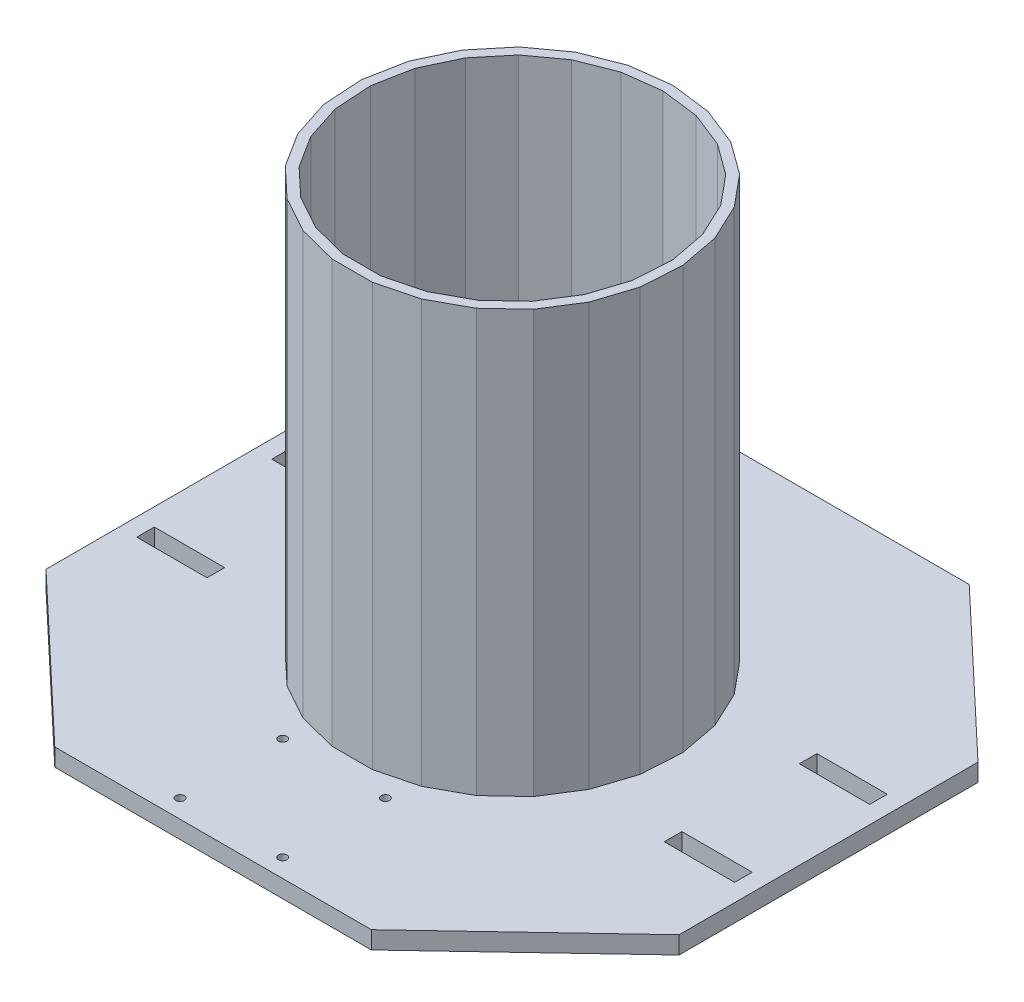
SolidWorks part; units mm, degrees
ref_plane "Front Plane" through (0, 0, 0) normal (0, 0, 1) x (1, 0, 0)
ref_plane "Top Plane" through (0, 0, 0) normal (0, 1, 0) x (1, 0, 0)
ref_plane "Right Plane" through (0, 0, 0) normal (1, 0, 0) x (0, 0, -1)
sketch "Sketch1" plane through (0, 0, 0) normal (0, 1, 0) x (1, 0, 0)
  line L1 (0, 0) -> (228.6, 0)
  line L2 (0, 0) -> (0, 215.9)
  line L3 (0, 215.9) -> (228.6, 215.9)
  line L4 (228.6, 0) -> (228.6, 215.9)
  dimension "D1" = 228.6
  dimension "D2" = 215.9
extrude "Boss-Extrude1" add sketch "Sketch1" along normal blind 6.35 contours L3 L4 L1 L2
sketch "Sketch14" plane through (0, 6.35, 0) normal (0, 1, 0) x (1, 0, 0)
  line L1 (0, 215.9) -> (228.6, 215.9) construction
  line L2 (0, 0) -> (228.6, 0) construction
  line L3 (0, 161.925) -> (228.6, 161.925) construction
  line L4 (0, 0) -> (0, 215.9) construction
  line L5 (228.6, 0) -> (228.6, 215.9) construction
  line L6 (0, 53.975) -> (228.6, 53.975) construction
  line L7 (57.15, 215.9) -> (57.15, 0) construction
  line L8 (171.45, 215.9) -> (171.45, 0) construction
sketch "Sketch13" plane through (0, 6.35, 0) normal (0, 1, 0) x (1, 0, 0)
  line L0 (0, 107.95) -> (228.6, 107.95) construction
  line L1 (0, 0) -> (0, 215.9) construction
  line L2 (228.6, 0) -> (228.6, 215.9) construction
  line L3 (0, 215.9) -> (0, 161.925)
  line L4 (0, 161.925) -> (57.15, 215.9)
  line L5 (57.15, 215.9) -> (0, 215.9)
  line L6 (114.3, 215.9) -> (114.3, 0) construction
  line L7 (0, 215.9) -> (228.6, 215.9) construction
  line L8 (0, 0) -> (228.6, 0) construction
  line L9 (228.6, 161.925) -> (171.45, 215.9)
  line L10 (228.6, 215.9) -> (228.6, 161.925)
  line L11 (171.45, 215.9) -> (228.6, 215.9)
  line L12 (228.6, 0) -> (228.6, 53.975)
  line L13 (171.45, 0) -> (228.6, 0)
  line L14 (228.6, 53.975) -> (171.45, 0)
  line L15 (0, 53.975) -> (57.15, 0)
  line L16 (0, 0) -> (0, 53.975)
  line L17 (57.15, 0) -> (0, 0)
sketch "Sketch8" plane through (0, 6.35, 0) normal (0, 1, 0) x (1, 0, 0)
  line L0 (0, 107.95) -> (228.6, 107.95) construction
  line L1 (6.35, 135.509) -> (31.75, 135.509)
  line L2 (6.35, 135.509) -> (6.35, 129.159)
  line L3 (6.35, 129.159) -> (31.75, 129.159)
  line L4 (31.75, 135.509) -> (31.75, 129.159)
  line L5 (0, 0) -> (0, 215.9) construction
  line L6 (228.6, 0) -> (228.6, 215.9) construction
  line L11 (114.3, 215.9) -> (114.3, 0) construction
  line L12 (0, 215.9) -> (228.6, 215.9) construction
  line L13 (0, 0) -> (228.6, 0) construction
  line L18 (222.25, 129.159) -> (196.85, 129.159)
  line L19 (196.85, 135.509) -> (196.85, 129.159)
  line L20 (222.25, 135.509) -> (196.85, 135.509)
  line L21 (222.25, 135.509) -> (222.25, 129.159)
  line L22 (222.25, 80.391) -> (222.25, 86.741)
  line L23 (222.25, 80.391) -> (196.85, 80.391)
  line L24 (196.85, 80.391) -> (196.85, 86.741)
  line L25 (222.25, 86.741) -> (196.85, 86.741)
  line L26 (6.35, 86.741) -> (31.75, 86.741)
  line L27 (31.75, 80.391) -> (31.75, 86.741)
  line L28 (6.35, 80.391) -> (31.75, 80.391)
  line L29 (6.35, 80.391) -> (6.35, 86.741)
  dimension "MotorMount1" = 25.4
  dimension "D2" = 6.35
  dimension "D1" = 21.209
  dimension "D5" = 6.35
extrude "Cut-Extrude2" cut sketch "Sketch8" against normal through all contours L2 L1 L4 L3 | L25 L24 L23 L22 | L18 L19 L20 L21 | L26 L27 L28 L29
sketch "Sketch11" plane through (0, 6.35, 0) normal (0, 1, 0) x (1, 0, 0)
  line L0 (114.3, 215.9) -> (114.3, 0) construction
  line L1 (0, 215.9) -> (228.6, 215.9) construction
  line L2 (0, 0) -> (228.6, 0) construction
  line L3 (92.71, 25.146) -> (135.89, 25.146) construction
  circle A0 centre (95.758, 6.604) radius 1.524
  circle A1 centre (132.842, 6.604) radius 1.524
  circle A2 centre (132.842, 43.688) radius 1.524
  circle A3 centre (95.758, 43.688) radius 1.524
extrude "Cut-Extrude4" cut sketch "Sketch11" against normal through all
extrude "Cut-Extrude5" cut sketch "Sketch13" against normal through all
sketch "Sketch18" plane through (0, 6.35, 0) normal (0, 1, 0) x (1, 0, 0)
  line L0 (114.3, 215.9) -> (114.3, 0) construction
  line L1 (57.15, 215.9) -> (171.45, 215.9) construction
  line L2 (57.15, 0) -> (171.45, 0) construction
  line L3 (0, 107.95) -> (228.6, 107.95) construction
  line L4 (0, 53.975) -> (0, 161.925) construction
  line L5 (228.6, 53.975) -> (228.6, 161.925) construction
  line L7 (114.3, 166.0959) -> (99.8397, 164.2691)
  line L8 (99.8397, 164.2691) -> (86.288, 158.9036)
  line L9 (86.288, 158.9036) -> (74.4964, 150.3365)
  line L10 (74.4964, 150.3365) -> (65.2058, 139.1061)
  line L11 (65.2058, 139.1061) -> (59, 125.9181)
  line L12 (59, 125.9181) -> (56.2688, 111.601)
  line L13 (56.2688, 111.601) -> (57.184, 97.0545)
  line L14 (57.184, 97.0545) -> (61.688, 83.1927)
  line L15 (61.688, 83.1927) -> (69.4978, 70.8864)
  line L16 (69.4978, 70.8864) -> (80.1227, 60.909)
  line L17 (80.1227, 60.909) -> (92.8951, 53.8873)
  line L18 (92.8951, 53.8873) -> (107.0124, 50.2626)
  line L19 (107.0124, 50.2626) -> (121.5876, 50.2626)
  line L20 (121.5876, 50.2626) -> (135.7049, 53.8873)
  line L21 (135.7049, 53.8873) -> (148.4773, 60.909)
  line L22 (148.4773, 60.909) -> (159.1022, 70.8864)
  line L23 (159.1022, 70.8864) -> (166.912, 83.1927)
  line L24 (166.912, 83.1927) -> (171.416, 97.0545)
  line L25 (171.416, 97.0545) -> (172.3312, 111.601)
  line L26 (172.3312, 111.601) -> (169.6, 125.9181)
  line L27 (169.6, 125.9181) -> (163.3942, 139.1061)
  line L28 (163.3942, 139.1061) -> (154.1036, 150.3365)
  line L29 (154.1036, 150.3365) -> (142.312, 158.9036)
  line L30 (142.312, 158.9036) -> (128.7603, 164.2691)
  line L31 (128.7603, 164.2691) -> (114.3, 166.0959)
  line L32 (114.3, 162.56) -> (100.719, 160.8443)
  line L33 (100.719, 160.8443) -> (87.9914, 155.8051)
  line L34 (87.9914, 155.8051) -> (76.9169, 147.759)
  line L35 (76.9169, 147.759) -> (68.1913, 137.2115)
  line L36 (68.1913, 137.2115) -> (62.3628, 124.8254)
  line L37 (62.3628, 124.8254) -> (59.7978, 111.379)
  line L38 (59.7978, 111.379) -> (60.6573, 97.7171)
  line L39 (60.6573, 97.7171) -> (64.8874, 84.6982)
  line L40 (64.8874, 84.6982) -> (72.2223, 73.1403)
  line L41 (72.2223, 73.1403) -> (82.201, 63.7696)
  line L42 (82.201, 63.7696) -> (94.1967, 57.1749)
  line L43 (94.1967, 57.1749) -> (107.4556, 53.7706)
  line L44 (107.4556, 53.7706) -> (121.1444, 53.7706)
  line L45 (121.1444, 53.7706) -> (134.4033, 57.1749)
  line L46 (134.4033, 57.1749) -> (146.399, 63.7696)
  line L47 (146.399, 63.7696) -> (156.3777, 73.1403)
  line L48 (156.3777, 73.1403) -> (163.7126, 84.6982)
  line L49 (163.7126, 84.6982) -> (167.9427, 97.7171)
  line L50 (167.9427, 97.7171) -> (168.8022, 111.379)
  line L51 (168.8022, 111.379) -> (166.2372, 124.8254)
  line L52 (166.2372, 124.8254) -> (160.4087, 137.2115)
  line L53 (160.4087, 137.2115) -> (151.6831, 147.759)
  line L54 (151.6831, 147.759) -> (140.6086, 155.8051)
  line L55 (140.6086, 155.8051) -> (127.881, 160.8443)
  line L56 (127.881, 160.8443) -> (114.3, 162.56)
  circle A0 centre (114.3, 107.95) radius 57.6874 construction
  circle A1 centre (114.3, 107.95) radius 54.61 construction
extrude "Boss-Extrude3" add sketch "Sketch18" along normal blind 152.4
sketch "Sketch20" plane through (0, 6.35, 0) normal (0, 1, 0) x (1, 0, 0)
  line L0 (61.7926, 83.0279) -> (64.8874, 84.6982)
  line L1 (61.688, 83.1927) -> (69.4978, 70.8864) construction
  line L2 (64.8874, 84.6982) -> (72.2223, 73.1403)
  line L3 (72.2223, 73.1403) -> (82.201, 63.7696)
  line L4 (82.201, 63.7696) -> (80.1227, 60.909)
  line L5 (80.1227, 60.909) -> (69.4978, 70.8864)
  line L6 (69.4978, 70.8864) -> (61.7926, 83.0279)
sketch "Sketch22" plane through (0, 6.35, 0) normal (0, 1, 0) x (1, 0, 0)
  line L0 (61.688, 83.1927) -> (64.8874, 84.6982)
  line L1 (64.8874, 84.6982) -> (72.2223, 73.1403)
  line L2 (72.2223, 73.1403) -> (69.4978, 70.8864)
  line L3 (69.4978, 70.8864) -> (61.688, 83.1927)
equation "\"GMaterial\" = \"MDF\""
equation "\"MDF\"= 0.25in"
equation "\"Foamcore\"= 0.1in"
equation "\"D1@Boss-Extrude1\"=\"GMaterial\""
equation "\"D2@Sketch8\"=\"GMaterial\""
equation "\"D1@Sketch8\"=1.67/2"
equation "\"D5@Sketch8\"=\"GMaterial\""
